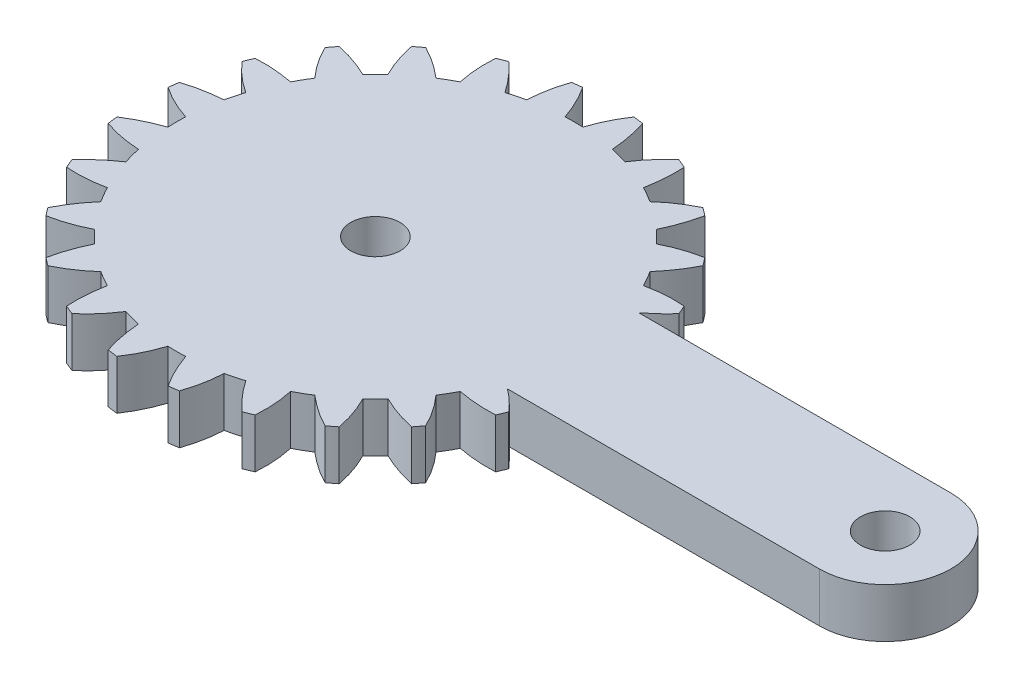
SolidWorks part; units mm, degrees
ref_plane "Front Plane" through (0, 0, 0) normal (0, 0, 1) x (1, 0, 0)
ref_plane "Top Plane" through (0, 0, 0) normal (0, 1, 0) x (1, 0, 0)
ref_plane "Right Plane" through (0, 0, 0) normal (1, 0, 0) x (0, 0, -1)
sketch "Sketch2" plane through (0, 0, 0) normal (0, 1, 0) x (1, 0, 0)
  line L0 (31, 4) -> (12.0129, 4)
  line L1 (31, -4) -> (12.0325, -4)
  line L2 (0, 0) -> (0, 12.09) construction
  line L3 (0, 0) -> (4.397, 16.4099) construction
  line L4 (0, 0) -> (-3.1291, 11.678) construction
  line L5 (-3.6882, 13.7644) -> (-4.4272, 16.5225) construction
  line L6 (0, 14.25) -> (0, 16.5009) construction
  line L7 (0, 0) -> (4.629, 11.1754) construction
  line L8 (4.629, 11.1754) -> (5.4532, 13.1653) construction
  circle A2 centre (31, 0) radius 1.5
  arc A3 (31, -4) -> (31, 4) centre (31, 0) ccw
  arc A12 (6.045, 10.4702) -> (5.5713, 10.7298) centre (0, 0) ccw
  arc A13 (3.6475, 11.5267) -> (3.1291, 11.678) centre (0, 0) ccw
  arc A81 (6.5065, 10.1899) -> (6.045, 10.4702) centre (0, 0) ccw
  arc A82 (8.5489, 8.5489) -> (8.1586, 8.9222) centre (0, 0) ccw
  circle A85 centre (0, 0) radius 1.5
  arc A87 (8.9148, 11.117) -> (8.4309, 11.4884) centre (0, 0) ccw
  arc A89 (8.9221, 8.1587) -> (8.5489, 8.5489) centre (0, 0) ccw
  arc A95 (10.4702, 6.045) -> (10.1898, 6.5066) centre (0, 0) ccw
  arc A97 (11.4884, 8.4309) -> (11.117, 8.9148) centre (0, 0) ccw
  arc A98 (10.7297, 5.5714) -> (10.4702, 6.045) centre (0, 0) ccw
  arc A100 (13.279, 5.1702) -> (13.0455, 5.7338) centre (0, 0) ccw
  arc A115 (10.4702, -6.045) -> (10.7298, -5.5713) centre (0, 0) ccw
  arc A117 (13.0455, -5.7338) -> (13.279, -5.1702) centre (0, 0) ccw
  arc A121 (5.7338, 13.0455) -> (5.1702, 13.279) centre (0, 0) ccw
  arc A161 (10.1899, -6.5065) -> (10.4702, -6.045) centre (0, 0) ccw
  arc A162 (8.5489, -8.5489) -> (8.9222, -8.1586) centre (0, 0) ccw
  arc A163 (11.117, -8.9148) -> (11.4884, -8.4309) centre (0, 0) ccw
  arc A164 (8.1587, -8.9221) -> (8.5489, -8.5489) centre (0, 0) ccw
  arc A165 (6.045, -10.4702) -> (6.5066, -10.1898) centre (0, 0) ccw
  arc A166 (8.4309, -11.4884) -> (8.9148, -11.117) centre (0, 0) ccw
  arc A167 (5.5714, -10.7297) -> (6.045, -10.4702) centre (0, 0) ccw
  arc A168 (3.1291, -11.678) -> (3.6476, -11.5266) centre (0, 0) ccw
  arc A169 (5.1702, -13.279) -> (5.7338, -13.0455) centre (0, 0) ccw
  arc A170 (2.6045, -11.8061) -> (3.1291, -11.678) centre (0, 0) ccw
  arc A171 (0, -12.09) -> (0.54, -12.0779) centre (0, 0) ccw
  arc A172 (1.5572, -14.1647) -> (2.162, -14.085) centre (0, 0) ccw
  arc A173 (-0.5399, -12.0779) -> (0, -12.09) centre (0, 0) ccw
  arc A174 (-3.1291, -11.678) -> (-2.6044, -11.8062) centre (0, 0) ccw
  arc A175 (-2.162, -14.085) -> (-1.5572, -14.1647) centre (0, 0) ccw
  arc A176 (-3.6475, -11.5267) -> (-3.1291, -11.678) centre (0, 0) ccw
  arc A177 (-6.045, -10.4702) -> (-5.5713, -10.7298) centre (0, 0) ccw
  arc A178 (-5.7338, -13.0455) -> (-5.1702, -13.279) centre (0, 0) ccw
  arc A179 (-6.5065, -10.1899) -> (-6.045, -10.4702) centre (0, 0) ccw
  arc A180 (-8.5489, -8.5489) -> (-8.1586, -8.9222) centre (0, 0) ccw
  arc A181 (-8.9148, -11.117) -> (-8.4309, -11.4884) centre (0, 0) ccw
  arc A182 (-8.9221, -8.1587) -> (-8.5489, -8.5489) centre (0, 0) ccw
  arc A183 (-10.4702, -6.045) -> (-10.1898, -6.5066) centre (0, 0) ccw
  arc A184 (-11.4884, -8.4309) -> (-11.117, -8.9148) centre (0, 0) ccw
  arc A185 (-10.7297, -5.5714) -> (-10.4702, -6.045) centre (0, 0) ccw
  arc A186 (-11.678, -3.1291) -> (-11.5266, -3.6476) centre (0, 0) ccw
  arc A187 (-13.279, -5.1702) -> (-13.0455, -5.7338) centre (0, 0) ccw
  arc A188 (-11.8061, -2.6045) -> (-11.678, -3.1291) centre (0, 0) ccw
  arc A189 (-12.09, 0) -> (-12.0779, -0.54) centre (0, 0) ccw
  arc A190 (-14.1647, -1.5572) -> (-14.085, -2.162) centre (0, 0) ccw
  arc A191 (-12.0779, 0.5399) -> (-12.09, 0) centre (0, 0) ccw
  arc A192 (-11.678, 3.1291) -> (-11.8062, 2.6044) centre (0, 0) ccw
  arc A193 (-14.085, 2.162) -> (-14.1647, 1.5572) centre (0, 0) ccw
  arc A194 (-11.5267, 3.6475) -> (-11.678, 3.1291) centre (0, 0) ccw
  arc A195 (-10.4702, 6.045) -> (-10.7298, 5.5713) centre (0, 0) ccw
  arc A196 (-13.0455, 5.7338) -> (-13.279, 5.1702) centre (0, 0) ccw
  arc A197 (-10.1899, 6.5065) -> (-10.4702, 6.045) centre (0, 0) ccw
  arc A198 (-8.5489, 8.5489) -> (-8.9222, 8.1586) centre (0, 0) ccw
  arc A199 (-11.117, 8.9148) -> (-11.4884, 8.4309) centre (0, 0) ccw
  arc A200 (-8.1587, 8.9221) -> (-8.5489, 8.5489) centre (0, 0) ccw
  arc A201 (-6.045, 10.4702) -> (-6.5066, 10.1898) centre (0, 0) ccw
  arc A202 (-8.4309, 11.4884) -> (-8.9148, 11.117) centre (0, 0) ccw
  arc A203 (-5.5714, 10.7297) -> (-6.045, 10.4702) centre (0, 0) ccw
  arc A204 (-3.1291, 11.678) -> (-3.6476, 11.5266) centre (0, 0) ccw
  arc A205 (-5.1702, 13.279) -> (-5.7338, 13.0455) centre (0, 0) ccw
  arc A206 (-2.6045, 11.8061) -> (-3.1291, 11.678) centre (0, 0) ccw
  arc A207 (0, 12.09) -> (-0.54, 12.0779) centre (0, 0) ccw
  arc A208 (-1.5572, 14.1647) -> (-2.162, 14.085) centre (0, 0) ccw
  arc A209 (0.5399, 12.0779) -> (0, 12.09) centre (0, 0) ccw
  arc A210 (3.1291, 11.678) -> (2.6044, 11.8062) centre (0, 0) ccw
  arc A211 (2.162, 14.085) -> (1.5572, 14.1647) centre (0, 0) ccw
  arc A212 (12.09, 0) -> (12.0779, 0.54) centre (0, 0) ccw [skipped]
  arc A213 (14.1647, 1.5572) -> (14.085, 2.162) centre (0, 0) ccw [skipped]
  arc A214 (12.0779, -0.5399) -> (12.09, 0) centre (0, 0) ccw [skipped]
  arc A215 (11.678, -3.1291) -> (11.8062, -2.6044) centre (0, 0) ccw [skipped]
  arc A216 (14.085, -2.162) -> (14.1647, -1.5572) centre (0, 0) ccw [skipped]
  arc A217 (11.5267, -3.6475) -> (11.678, -3.1291) centre (0, 0) ccw [skipped]
  arc A218 (11.8061, 2.6045) -> (11.678, 3.1291) centre (0, 0) ccw [skipped]
  arc A219 (11.678, 3.1291) -> (11.5266, 3.6476) centre (0, 0) ccw [skipped]
  spline S0 degree 3 poles (8.9148, 11.117) (8.7604, 10.3435) (8.4826, 9.6001) (8.1586, 8.9222) knots 0.154713 0.154713 0.154713 0.154713 1 1 1 1
  spline S1 degree 3 poles (6.5065, 10.1899) (7.0658, 10.6979) (7.7126, 11.1471) (8.4309, 11.4884) knots 0 0 0 0 0.845227 0.845227 0.845227 0.845227
  spline S2 degree 3 poles (11.4884, 8.4309) (11.139, 7.7237) (10.6783, 7.0775) (10.1898, 6.5066) knots 0.154713 0.154713 0.154713 0.154713 1 1 1 1
  spline S3 degree 3 poles (8.9221, 8.1587) (9.5939, 8.5047) (10.3348, 8.7711) (11.117, 8.9148) knots 0 0 0 0 0.845227 0.845227 0.845227 0.845227
  spline S4 degree 3 poles (3.6475, 11.5267) (4.0562, 12.1622) (4.5647, 12.7634) (5.1702, 13.279) knots 0 0 0 0 0.845227 0.845227 0.845227 0.845227
  spline S5 degree 3 poles (5.7338, 13.0455) (5.7848, 12.2584) (5.7089, 11.4685) (5.5713, 10.7298) knots 0.154713 0.154713 0.154713 0.154713 1 1 1 1
  spline S6 degree 3 poles (13.279, 5.1702) (12.8955, 4.7335) (12.4622, 4.3445) (12.0129, 4) knots 0.154713 0.154713 0.154713 0.154713 0.77749 0.77749 0.77749 0.77749
  spline S7 degree 3 poles (10.7297, 5.5714) (11.4681, 5.7318) (12.2528, 5.7974) (13.0455, 5.7338) knots 0 0 0 0 0.845227 0.845227 0.845227 0.845227
  spline S12 degree 3 poles (13.0455, -5.7338) (12.2584, -5.7848) (11.4685, -5.7089) (10.7298, -5.5713) knots 0.154713 0.154713 0.154713 0.154713 1 1 1 1
  spline S13 degree 3 poles (12.0325, -4) (12.4803, -4.3376) (12.9025, -4.728) (13.279, -5.1702) knots 0.228019 0.228019 0.228019 0.228019 0.845227 0.845227 0.845227 0.845227
  spline S14 degree 3 poles (11.117, -8.9148) (10.3435, -8.7604) (9.6001, -8.4826) (8.9222, -8.1586) knots 0.154713 0.154713 0.154713 0.154713 1 1 1 1
  spline S15 degree 3 poles (10.1899, -6.5065) (10.6979, -7.0658) (11.1471, -7.7126) (11.4884, -8.4309) knots 0 0 0 0 0.845227 0.845227 0.845227 0.845227
  spline S16 degree 3 poles (8.4309, -11.4884) (7.7237, -11.139) (7.0775, -10.6783) (6.5066, -10.1898) knots 0.154713 0.154713 0.154713 0.154713 1 1 1 1
  spline S17 degree 3 poles (8.1587, -8.9221) (8.5047, -9.5939) (8.7711, -10.3348) (8.9148, -11.117) knots 0 0 0 0 0.845227 0.845227 0.845227 0.845227
  spline S18 degree 3 poles (5.1702, -13.279) (4.5775, -12.7584) (4.0726, -12.1462) (3.6476, -11.5266) knots 0.154713 0.154713 0.154713 0.154713 1 1 1 1
  spline S19 degree 3 poles (5.5714, -10.7297) (5.7318, -11.4681) (5.7974, -12.2528) (5.7338, -13.0455) knots 0 0 0 0 0.845227 0.845227 0.845227 0.845227
  spline S20 degree 3 poles (1.5572, -14.1647) (1.1194, -13.5085) (0.7902, -12.7864) (0.54, -12.0779) knots 0.154713 0.154713 0.154713 0.154713 1 1 1 1
  spline S21 degree 3 poles (2.6045, -11.8061) (2.5683, -12.5609) (2.4286, -13.3358) (2.162, -14.085) knots 0 0 0 0 0.845227 0.845227 0.845227 0.845227
  spline S22 degree 3 poles (-2.162, -14.085) (-2.415, -13.3379) (-2.5461, -12.5553) (-2.6044, -11.8062) knots 0.154713 0.154713 0.154713 0.154713 1 1 1 1
  spline S23 degree 3 poles (-0.5399, -12.0779) (-0.7702, -12.7976) (-1.1057, -13.5099) (-1.5572, -14.1647) knots 0 0 0 0 0.845227 0.845227 0.845227 0.845227
  spline S24 degree 3 poles (-5.7338, -13.0455) (-5.7848, -12.2584) (-5.7089, -11.4685) (-5.5713, -10.7298) knots 0.154713 0.154713 0.154713 0.154713 1 1 1 1
  spline S25 degree 3 poles (-3.6475, -11.5267) (-4.0562, -12.1622) (-4.5647, -12.7634) (-5.1702, -13.279) knots 0 0 0 0 0.845227 0.845227 0.845227 0.845227
  spline S26 degree 3 poles (-8.9148, -11.117) (-8.7604, -10.3435) (-8.4826, -9.6001) (-8.1586, -8.9222) knots 0.154713 0.154713 0.154713 0.154713 1 1 1 1
  spline S27 degree 3 poles (-6.5065, -10.1899) (-7.0658, -10.6979) (-7.7126, -11.1471) (-8.4309, -11.4884) knots 0 0 0 0 0.845227 0.845227 0.845227 0.845227
  spline S28 degree 3 poles (-11.4884, -8.4309) (-11.139, -7.7237) (-10.6783, -7.0775) (-10.1898, -6.5066) knots 0.154713 0.154713 0.154713 0.154713 1 1 1 1
  spline S29 degree 3 poles (-8.9221, -8.1587) (-9.5939, -8.5047) (-10.3348, -8.7711) (-11.117, -8.9148) knots 0 0 0 0 0.845227 0.845227 0.845227 0.845227
  spline S30 degree 3 poles (-13.279, -5.1702) (-12.7584, -4.5775) (-12.1462, -4.0726) (-11.5266, -3.6476) knots 0.154713 0.154713 0.154713 0.154713 1 1 1 1
  spline S31 degree 3 poles (-10.7297, -5.5714) (-11.4681, -5.7318) (-12.2528, -5.7974) (-13.0455, -5.7338) knots 0 0 0 0 0.845227 0.845227 0.845227 0.845227
  spline S32 degree 3 poles (-14.1647, -1.5572) (-13.5085, -1.1194) (-12.7864, -0.7902) (-12.0779, -0.54) knots 0.154713 0.154713 0.154713 0.154713 1 1 1 1
  spline S33 degree 3 poles (-11.8061, -2.6045) (-12.5609, -2.5683) (-13.3358, -2.4286) (-14.085, -2.162) knots 0 0 0 0 0.845227 0.845227 0.845227 0.845227
  spline S34 degree 3 poles (-14.085, 2.162) (-13.3379, 2.415) (-12.5553, 2.5461) (-11.8062, 2.6044) knots 0.154713 0.154713 0.154713 0.154713 1 1 1 1
  spline S35 degree 3 poles (-12.0779, 0.5399) (-12.7976, 0.7702) (-13.5099, 1.1057) (-14.1647, 1.5572) knots 0 0 0 0 0.845227 0.845227 0.845227 0.845227
  spline S36 degree 3 poles (-13.0455, 5.7338) (-12.2584, 5.7848) (-11.4685, 5.7089) (-10.7298, 5.5713) knots 0.154713 0.154713 0.154713 0.154713 1 1 1 1
  spline S37 degree 3 poles (-11.5267, 3.6475) (-12.1622, 4.0562) (-12.7634, 4.5647) (-13.279, 5.1702) knots 0 0 0 0 0.845227 0.845227 0.845227 0.845227
  spline S38 degree 3 poles (-11.117, 8.9148) (-10.3435, 8.7604) (-9.6001, 8.4826) (-8.9222, 8.1586) knots 0.154713 0.154713 0.154713 0.154713 1 1 1 1
  spline S39 degree 3 poles (-10.1899, 6.5065) (-10.6979, 7.0658) (-11.1471, 7.7126) (-11.4884, 8.4309) knots 0 0 0 0 0.845227 0.845227 0.845227 0.845227
  spline S40 degree 3 poles (-8.4309, 11.4884) (-7.7237, 11.139) (-7.0775, 10.6783) (-6.5066, 10.1898) knots 0.154713 0.154713 0.154713 0.154713 1 1 1 1
  spline S41 degree 3 poles (-8.1587, 8.9221) (-8.5047, 9.5939) (-8.7711, 10.3348) (-8.9148, 11.117) knots 0 0 0 0 0.845227 0.845227 0.845227 0.845227
  spline S42 degree 3 poles (-5.1702, 13.279) (-4.5775, 12.7584) (-4.0726, 12.1462) (-3.6476, 11.5266) knots 0.154713 0.154713 0.154713 0.154713 1 1 1 1
  spline S43 degree 3 poles (-5.5714, 10.7297) (-5.7318, 11.4681) (-5.7974, 12.2528) (-5.7338, 13.0455) knots 0 0 0 0 0.845227 0.845227 0.845227 0.845227
  spline S44 degree 3 poles (-1.5572, 14.1647) (-1.1194, 13.5085) (-0.7902, 12.7864) (-0.54, 12.0779) knots 0.154713 0.154713 0.154713 0.154713 1 1 1 1
  spline S45 degree 3 poles (-2.6045, 11.8061) (-2.5683, 12.5609) (-2.4286, 13.3358) (-2.162, 14.085) knots 0 0 0 0 0.845227 0.845227 0.845227 0.845227
  spline S46 degree 3 poles (2.162, 14.085) (2.415, 13.3379) (2.5461, 12.5553) (2.6044, 11.8062) knots 0.154713 0.154713 0.154713 0.154713 1 1 1 1
  spline S47 degree 3 poles (0.5399, 12.0779) (0.7702, 12.7976) (1.1057, 13.5099) (1.5572, 14.1647) knots 0 0 0 0 0.845227 0.845227 0.845227 0.845227
  point P11 (0, 12.09)
  point P15 (-3.1291, 11.678)
  point P167 (0, 0)
  point P177 (0, 0)
  dimension "D1" = 3
  dimension "D2" = 8
  dimension "D7" = 24
  dimension "D8" = 3.1561
  dimension "D6" = 24
  dimension "D15" = 0.61
  dimension "D3" = 31
  dimension "D4" = 15
  dimension "D5" = 15
  dimension "D16" = 7.5
  dimension "D17" = 180
extrude "Boss-Extrude1" add sketch "Sketch2" along normal blind 3
scale "Scale1" scale about centroid uniform scaling yes scale factor 1.8
